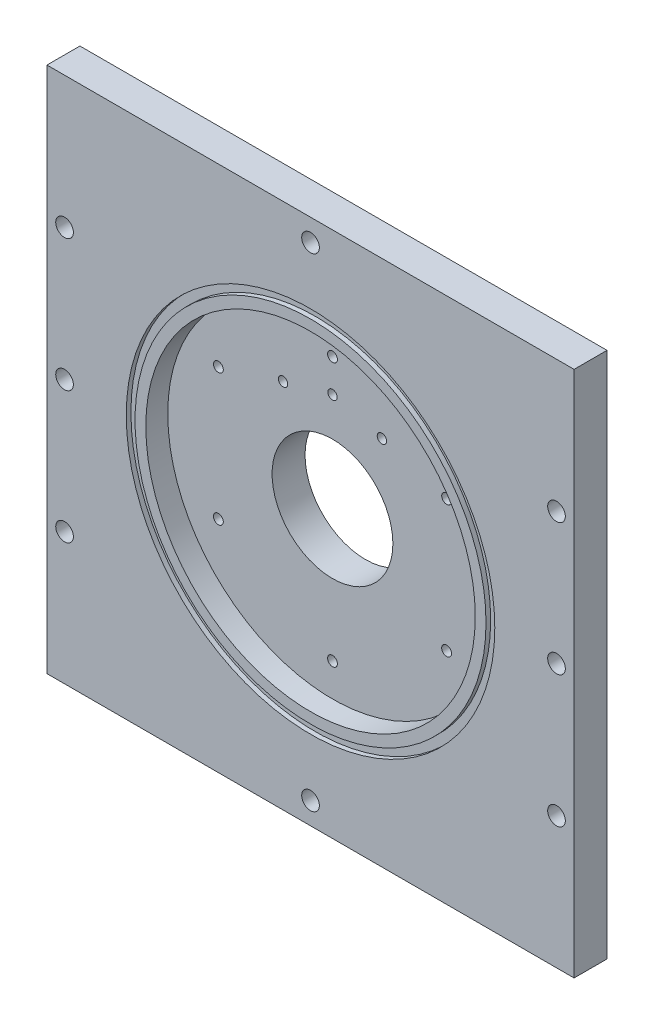
SolidWorks part; units mm, degrees
ref_plane "Front Plane" through (0, 0, 0) normal (0, 0, 1) x (1, 0, 0)
ref_plane "Top Plane" through (0, 0, 0) normal (0, 1, 0) x (1, 0, 0)
ref_plane "Right Plane" through (0, 0, 0) normal (1, 0, 0) x (0, 0, -1)
ref_plane "Plane1" through (0, 0, 0) normal (0, 0, -1) x (-1, 0, 0)
sketch "Sketch1" plane through (0, 0, 0) normal (0, 0, -1) x (-1, 0, 0)
  line L0 (76.2, 76.2) -> (-76.2, 76.2)
  line L1 (-76.2, 76.2) -> (-76.2, -76.2)
  line L2 (-76.2, -76.2) -> (76.2, -76.2)
  line L3 (76.2, -76.2) -> (76.2, 76.2)
extrude "Boss-Extrude1" add sketch "Sketch1" against normal blind 9.525
sketch "Sketch4" plane through (0, 0, 0) normal (0, 1, 0) x (1, 0, 0)
  line L0 (63.5, 6.35) -> (0, 6.35)
  line L1 (0, 6.35) -> (0, 0)
  line L2 (0, 0) -> (63.5, 0)
  line L3 (63.5, 0) -> (63.5, 6.35)
  line L4 (0, 6.35) -> (0, 0) construction
  line L5 (-76.2, 0) -> (76.2, 0) construction
  dimension "D1" = 6.35
  dimension "D2" = 63.5
  dimension "D3" = 0
revolve "Revolve1" add sketch "Sketch4" angle 360 about L4
hole_wizard "CBORE for #10 Socket Head Cap Screw1" positions "Sketch7" profile "Sketch6" counterbore size "#10" standard "ANSI Inch" end condition through all
sketch "Sketch7" plane through (0, 0, 0) normal (0, 0, -1) x (-1, 0, 0)
  point P0 (71.12, 38.1)
  point P1 (71.12, -38.1)
  point P2 (-71.12, 38.1)
  point P3 (-71.12, -38.1)
  point P4 (0, 69.85)
  point P5 (0, -69.85)
  point P6 (71.12, 0)
  point P7 (-71.12, 0)
sketch "Sketch6" plane through (-71.12, 38.1, 0) normal (1, 0, 0) x (0, 1, 0)
  line L0 (0, 0) -> (0, 9.525)
  line L1 (0, 9.525) -> (2.5527, 9.525)
  line L3 (2.5527, 9.525) -> (2.5527, 4.826)
  line L4 (2.5527, 4.826) -> (4.7625, 4.826)
  line L5 (4.7625, 4.826) -> (4.7625, 0)
  line L7 (4.7625, 0) -> (0, 0)
  line L11 (0, -6.35) -> (0, 107.95) construction
  dimension "Thru Hole Dia." = 5.1054
  dimension "Thru Hole Depth" = 9.525
  dimension "C'Bore Dia." = 9.525
  dimension "C'Bore Depth" = 4.826
sketch "Sketch19" plane through (0, 0, -6.35) normal (0, 0, -1) x (-1, 0, 0)
  line L0 (-36.3614, 15.494) -> (17.3114, -15.494)
  line L1 (-36.3614, -15.494) -> (17.3114, 15.494)
  line L2 (-9.525, 30.988) -> (-9.525, -30.988)
  circle A0 centre (-9.525, 0) radius 5.5273
sketch "Sketch21" [suppressed] plane through (0, 0, 9.525) normal (0, 0, 1) x (1, 0, 0)
  line L0 (0, 69.85) -> (0, -69.85)
sketch "Sketch22" plane through (0, 0, 9.525) normal (0, 0, 1) x (1, 0, 0)
  circle A0 centre (0, 0) radius 47.625
  dimension "D1" = 95.25
extrude "Cut-Extrude3" cut sketch "Sketch22" against normal blind 6.35
sketch "Sketch23" plane through (0, 0, 9.525) normal (0, 0, 1) x (1, 0, 0)
  circle A0 centre (0, 0) radius 53.2765
  circle A1 centre (0, 0) radius 50.7365
  dimension "D1" = 106.553
  dimension "D2" = 2.54
extrude "Cut-Extrude4" cut sketch "Sketch23" against normal blind 1.3462
sketch "Sketch24" plane through (0, 0, 3.175) normal (0, 0, 1) x (1, 0, 0)
  circle A0 centre (0, 0) radius 17.4625
  dimension "D1" = 34.925
extrude "Cut-Extrude5" cut sketch "Sketch24" against normal blind 25.4
hole_wizard "#4-40 Tapped Hole1" positions "Sketch26" profile "Sketch25" tap size "#4-40" standard "ANSI Inch"
sketch "Sketch26" plane through (0, 0, 3.175) normal (0, 0, 1) x (1, 0, 0)
  line L0 (0, 0) -> (0, 38.1)
  point P2 (0, 38.1)
  dimension "D1" = 38.1
sketch "Sketch25" plane through (0, 38.1, 3.175) normal (1, 0, 0) x (0, -1, 0)
  line L0 (0, 0) -> (0, 8.2738)
  line L1 (0, 8.2738) -> (1.1303, 7.5946)
  line L2 (1.1303, 7.5946) -> (1.1303, 5.6896)
  line L3 (1.1303, 5.6896) -> (1.4224, 5.6896)
  line L4 (1.4224, 5.6896) -> (1.4224, 0)
  line L5 (1.4224, 0) -> (0, 0)
  line L10 (0, 8.2738) -> (-1.1303, 7.5946) construction
  line L11 (0, -6.35) -> (0, 107.95) construction
  dimension "Tap Drill Dia." = 2.2606
  dimension "Tap Drill Depth" = 7.5946
  dimension "Thread Major Dia." = 2.8448
  dimension "Thread Depth" = 5.6896
  dimension "Drill Angle" = 118
pattern_circular "CirPattern1" count 6 over 360 about axis through (0, 0, 0) along (0, 0, 1) of "#4-40 Tapped Hole1"
sketch "Sketch27" plane through (0, 0, 3.175) normal (0, 0, 1) x (1, 0, 0)
  line L0 (0, 38.1) -> (0, 24.13)
sketch "Sketch28" plane through (0, 0, 3.175) normal (0, 0, 1) x (1, 0, 0)
  circle A0 centre (0, 28.575) radius 0.635
  dimension "D1" = 1.27
  dimension "D2" = 28.575
extrude "Cut-Extrude6" cut sketch "Sketch28" against normal through all
hole_wizard "#6-32 Tapped Hole1" positions "Sketch30" profile "Sketch29" tap size "#6-32" standard "ANSI Inch" end condition through all
sketch "Sketch30" plane through (0, 0, 3.175) normal (0, 0, 1) x (1, 0, 0)
  point P0 (0, 28.575)
sketch "Sketch29" plane through (0, 28.575, 3.175) normal (1, 0, 0) x (0, -1, 0)
  line L0 (0, 0) -> (0, 9.525)
  line L1 (0, 9.525) -> (1.3525, 9.525)
  line L2 (1.3525, 9.525) -> (1.3525, 0)
  line L5 (1.3525, 0) -> (0, 0)
  line L11 (0, -6.35) -> (0, 107.95) construction
  dimension "Thru Tap Drill Dia." = 2.7051
  dimension "Thru Tap Drill Depth" = 9.525
cosmetic thread "Hole Thread1" parameters "D2"=3.5052
pattern_circular "CirPattern2" count 2 every 30 about axis through (0, 0, 3.175) along (0, 0, 1) of "Cut-Extrude6", "#6-32 Tapped Hole1"
pattern_circular "CirPattern3" count 2 every 30 about axis through (0, 0, 3.175) along (0, 0, 1) of "Cut-Extrude6", "#6-32 Tapped Hole1"
